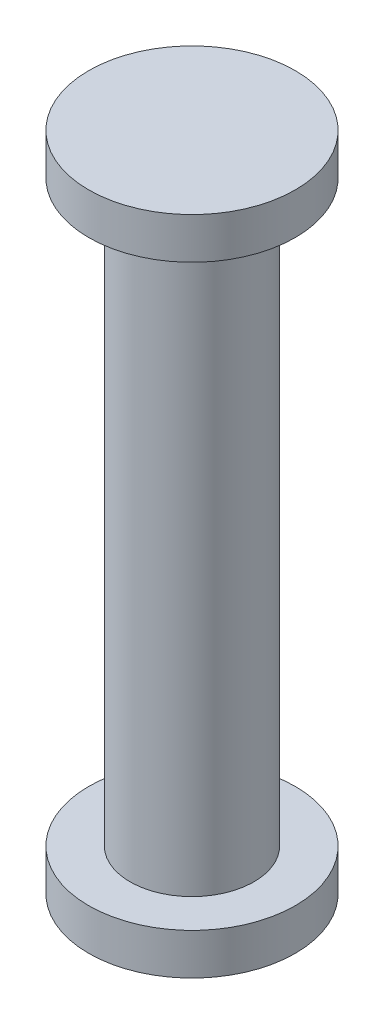
SolidWorks part; units mm, degrees
ref_plane "Front Plane" through (0, 0, 0) normal (0, 0, 1) x (1, 0, 0)
ref_plane "Top Plane" through (0, 0, 0) normal (0, 1, 0) x (1, 0, 0)
ref_plane "Right Plane" through (0, 0, 0) normal (1, 0, 0) x (0, 0, -1)
sketch "Sketch1" plane through (0, 0, 0) normal (0, 0, 1) x (1, 0, 0)
  line L0 (0, 0) -> (0, 16)
  line L1 (0, 16) -> (-2.5, 16)
  line L2 (-2.5, 16) -> (-2.5, 15)
  line L3 (-2.5, 15) -> (-1.5, 15)
  line L4 (-1.5, 15) -> (-1.5, 1)
  line L5 (-1.5, 1) -> (-2.5, 1)
  line L6 (-2.5, 1) -> (-2.5, 0)
  line L7 (-2.5, 0) -> (0, 0)
  dimension "D1" = 16
  dimension "D2" = 1
  dimension "D3" = 2.5
  dimension "D4" = 1.5
  dimension "D5" = 1
revolve "Revolve1" add sketch "Sketch1" angle 360 about L0
